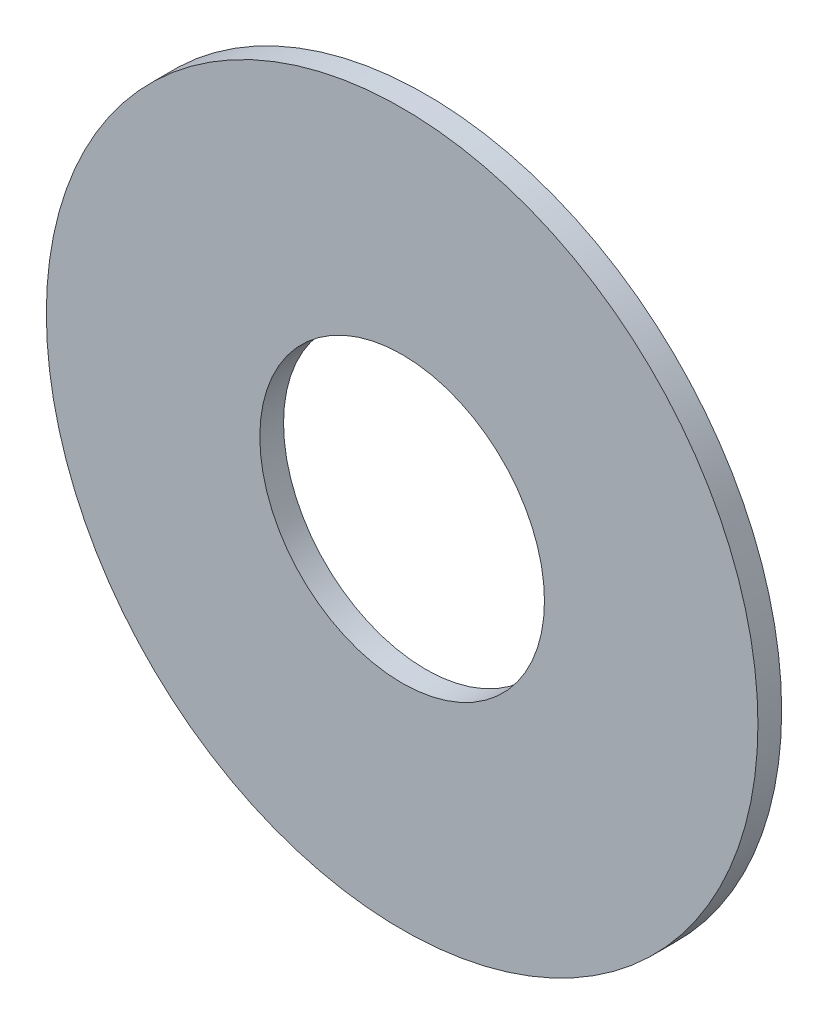
SolidWorks part; units mm, degrees
material "Сталь ШХ15 ГОСТ 801-78"
ref_plane "Plane1" through (0, 0, 0) normal (0, 0, 1) x (1, 0, 0)
ref_plane "Plane2" through (0, 0, 0) normal (0, 1, 0) x (1, 0, 0)
ref_plane "Plane3" through (0, 0, 0) normal (1, 0, 0) x (0, 0, -1)
sketch "Эскиз1" plane through (0, 0, 0) normal (0, 0, 1) x (1, 0, 0)
  circle A0 centre (0, 0) radius 15
  circle A1 centre (0, 0) radius 6
  dimension "D1" = 30
  dimension "D2" = 12
extrude "Бобышка-Вытянуть1" add sketch "Эскиз1" along normal blind 1 contours A1 | A0
